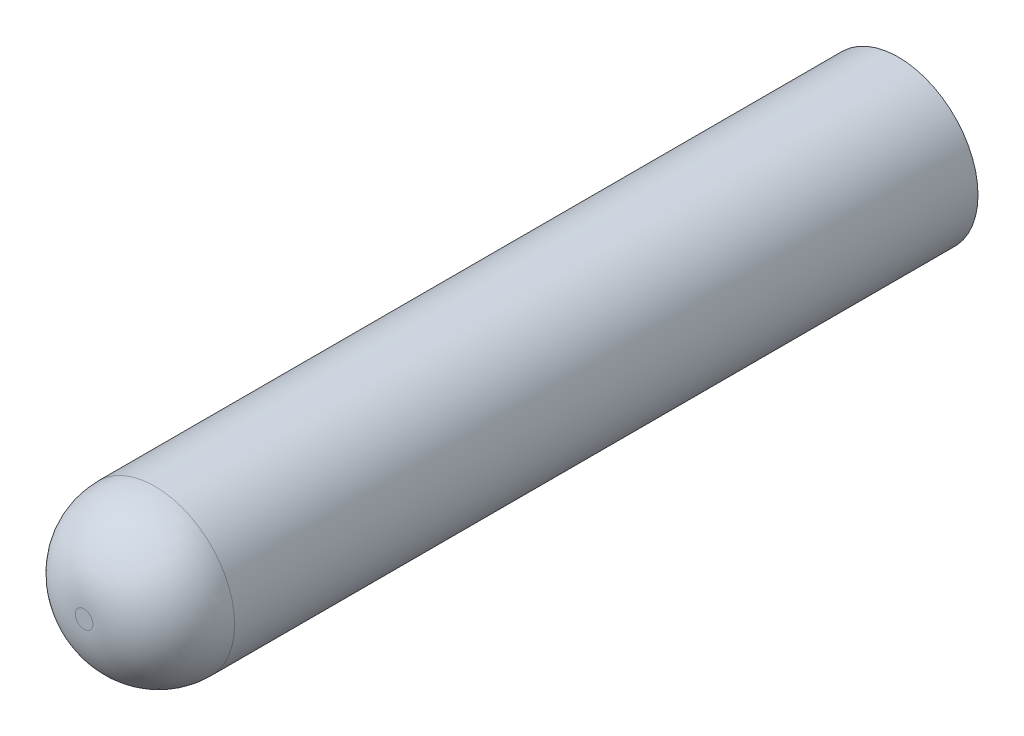
SolidWorks part; units mm, degrees
ref_plane "Front Plane" through (0, 0, 0) normal (0, 0, 1) x (1, 0, 0)
ref_plane "Top Plane" through (0, 0, 0) normal (0, 1, 0) x (1, 0, 0)
ref_plane "Right Plane" through (0, 0, 0) normal (1, 0, 0) x (0, 0, -1)
sketch "草图1" plane through (0, 0, 0) normal (0, 0, 1) x (1, 0, 0)
  circle A0 centre (0, 0) radius 2.25
  dimension "D1" = 4.5
extrude "凸台-拉伸2" add sketch "草图1" along normal blind 23
sketch "草图7" plane through (0, 0, 0) normal (0, 0, 1) x (1, 0, 0)
  line L1 (1.2, -1.2) -> (-1.2, -1.2)
  line L2 (1.2, -1.2) -> (1.2, 1.2)
  line L3 (1.2, 1.2) -> (-1.2, 1.2)
  line L4 (-1.2, -1.2) -> (-1.2, 1.2)
  line L5 (1.2, -1.2) -> (-1.2, 1.2) construction
  line L6 (1.2, 1.2) -> (-1.2, -1.2) construction
  point P0 (0, 0)
  dimension "D1" = 2.4
  dimension "D2" = 2.4
extrude "切除-拉伸3" cut sketch "草图7" along normal blind 4.5 from surface at 0 starting at face at (2.25, 0, 0)
fillet "圆角2" radius 2 1 edges at (2.25, 0, 23)
